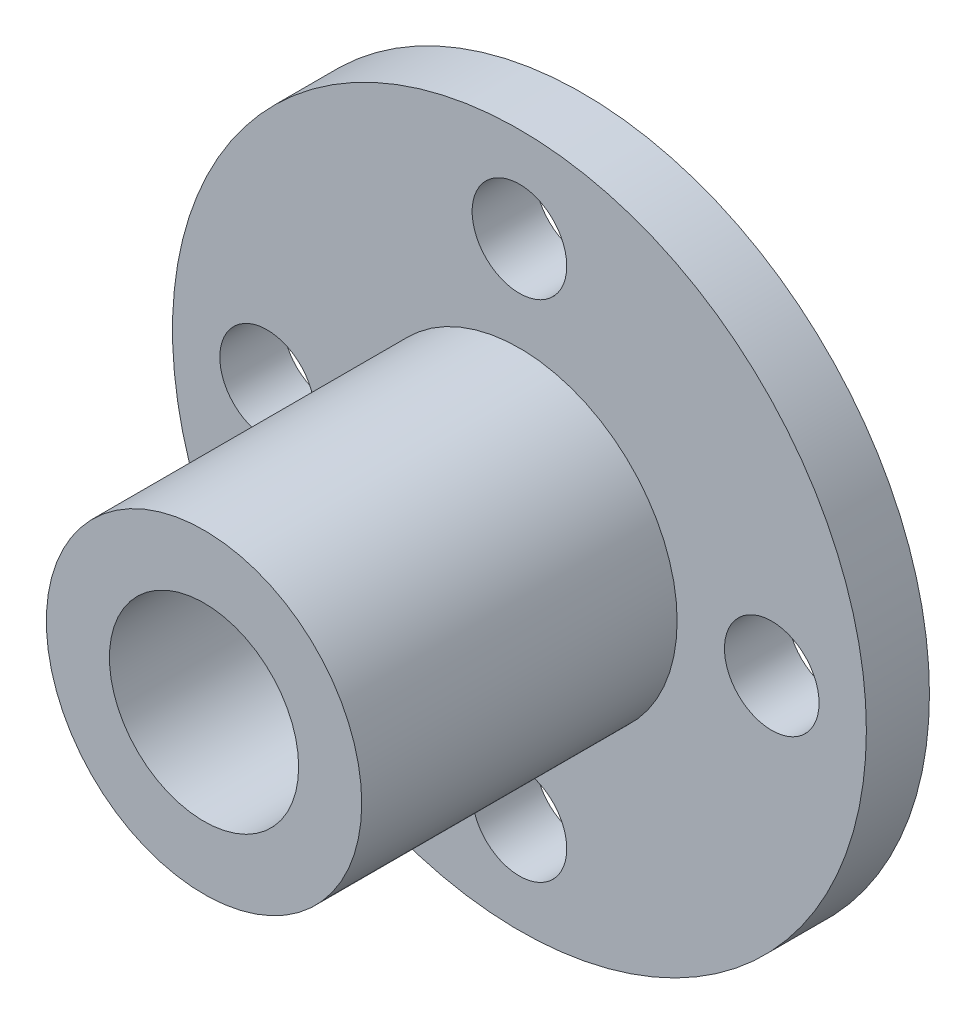
SolidWorks part; units mm, degrees
ref_plane "前视基准面" through (0, 0, 0) normal (0, 0, 1) x (1, 0, 0)
ref_plane "上视基准面" through (0, 0, 0) normal (0, 1, 0) x (1, 0, 0)
ref_plane "右视基准面" through (0, 0, 0) normal (1, 0, 0) x (0, 0, -1)
sketch "草图1" plane through (0, 0, 0) normal (0, 0, 1) x (1, 0, 0)
  circle A0 centre (0, 0) radius 11
  dimension "D1" = 22
extrude "凸台-拉伸1" add sketch "草图1" along normal blind 2
sketch "草图2" plane through (0, 0, 2) normal (0, 0, 1) x (1, 0, 0)
  circle A0 centre (0, 0) radius 5
  dimension "D1" = 10
extrude "凸台-拉伸2" add sketch "草图2" along normal blind 10
sketch "草图4" plane through (0, 0, 12) normal (0, 0, 1) x (1, 0, 0)
  circle A0 centre (0, 0) radius 3
  dimension "D1" = 6
extrude "切除-拉伸2" cut sketch "草图4" against normal through all
sketch "草图5" plane through (0, 0, 2) normal (0, 0, 1) x (1, 0, 0)
  circle A1 centre (-8, 0) radius 1.5
  circle A2 centre (0, 8) radius 1.5
  circle A3 centre (8, 0) radius 1.5
  circle A4 centre (0, -8) radius 1.5
  point P13 (0, 0)
  dimension "D1" = 16
  dimension "D2" = 3
  dimension "D3" = 4
extrude "切除-拉伸3" cut sketch "草图5" against normal up to next
